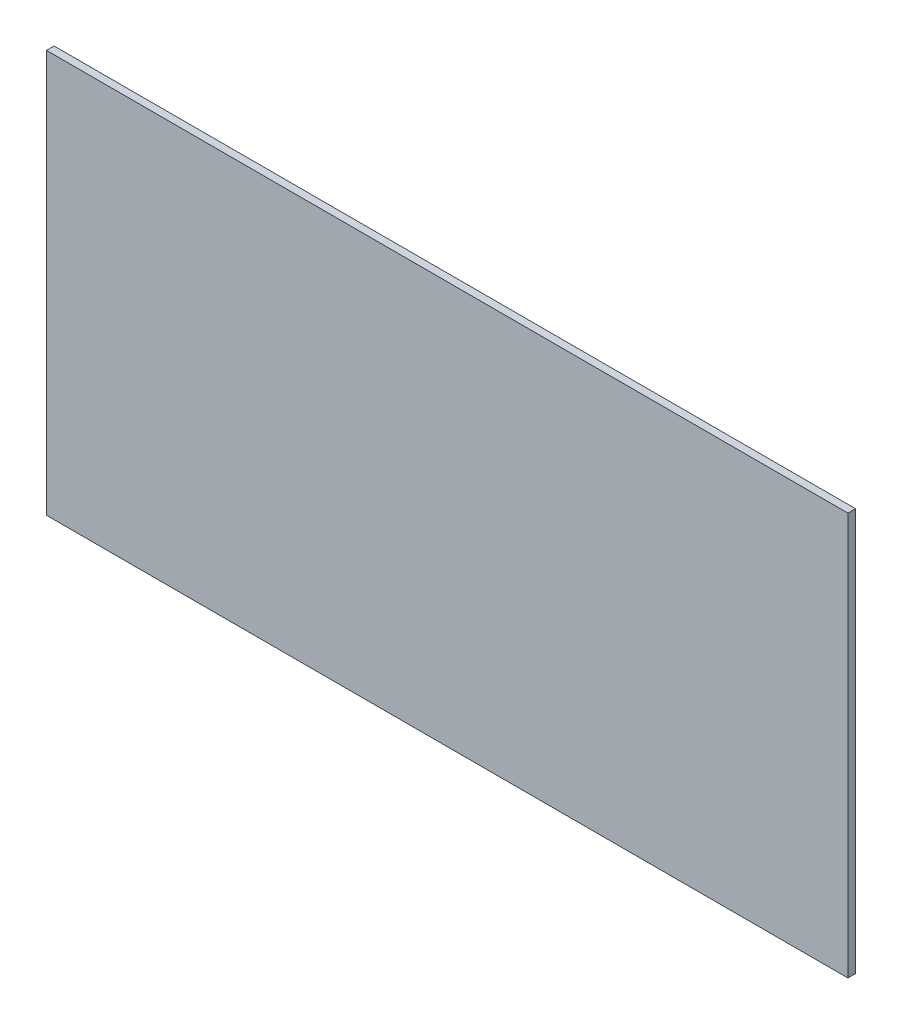
SolidWorks part; units mm, degrees
material "ABS PC"
ref_plane "Front Plane" through (0, 0, 0) normal (0, 0, 1) x (1, 0, 0)
ref_plane "Top Plane" through (0, 0, 0) normal (0, 1, 0) x (1, 0, 0)
ref_plane "Right Plane" through (0, 0, 0) normal (1, 0, 0) x (0, 0, -1)
sketch "Sketch1" plane through (0, 0, 0) normal (0, 0, 1) x (1, 0, 0)
  line L5 (16.4219, 202.5496) -> (16.4219, 195.8186)
  line L8 (29.8204, 202.5496) -> (16.4219, 202.5496)
  line L10 (16.4219, 195.8186) -> (29.8204, 195.8186)
  line L11 (29.8204, 195.8186) -> (29.8204, 202.5496)
extrude "Boss-Extrude1" add sketch "Sketch1" along normal blind 0.127
